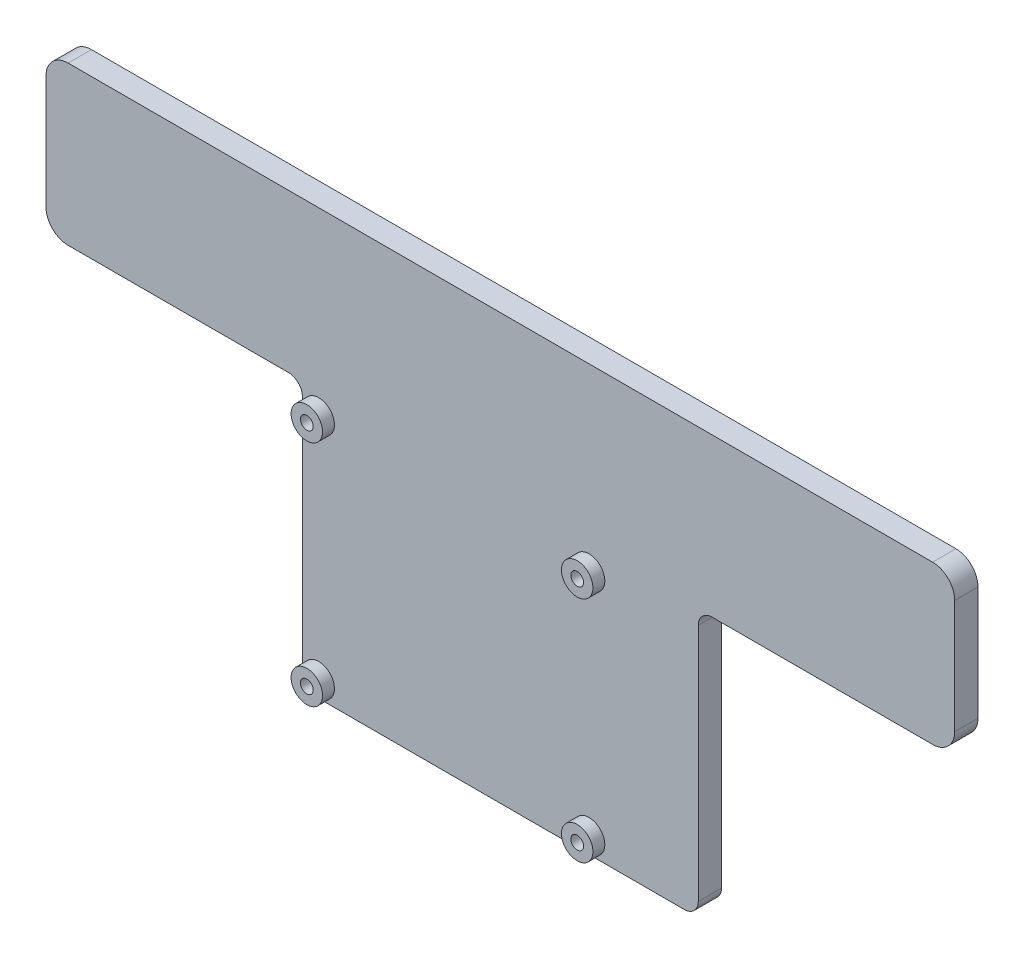
SolidWorks part; units mm, degrees
ref_plane "Ebene vorne" through (0, 0, 0) normal (0, 0, 1) x (1, 0, 0)
ref_plane "Ebene oben" through (0, 0, 0) normal (0, 1, 0) x (1, 0, 0)
ref_plane "Ebene rechts" through (0, 0, 0) normal (1, 0, 0) x (0, 0, -1)
sketch "Grundform" plane through (0, 0, 0) normal (0, 0, 1) x (1, 0, 0)
  line L0 (-93.287, 40.7816) -> (92.1707, 40.7816)
  line L2 (92.1707, 6.9168) -> (44.9039, 6.9168)
  line L4 (38.9039, -50.3878) -> (-40.0203, -50.3878)
  line L6 (-46.0203, 6.9168) -> (-93.287, 6.9168)
  line L8 (-0.5582, 76.8719) -> (-0.5582, -104.5887) construction
  line L9 (-98.0291, 36.0396) -> (-98.0291, 11.6588)
  line L10 (96.9127, 36.0396) -> (96.9127, 11.6588)
  line L11 (-43.0203, 3.9168) -> (-43.0203, -47.3878)
  line L12 (41.9039, -47.3878) -> (41.9039, 3.9168)
  line L13 (38.9039, -50.3878) -> (-40.0203, -50.3878) construction
  line L14 (41.9039, 2.6122) -> (41.9039, -47.3878) construction
  arc A0 (-93.287, 40.7816) -> (-98.0291, 36.0396) centre (-93.287, 36.0396) ccw
  arc A1 (-93.287, 6.9168) -> (-98.0291, 11.6588) centre (-93.287, 11.6588) cw
  arc A2 (92.1707, 40.7816) -> (96.9127, 36.0396) centre (92.1707, 36.0396) cw
  arc A3 (92.1707, 6.9168) -> (96.9127, 11.6588) centre (92.1707, 11.6588) ccw
  arc A4 (-46.0203, 6.9168) -> (-43.0203, 3.9168) centre (-46.0203, 3.9168) cw
  arc A5 (44.9039, 6.9168) -> (41.9039, 3.9168) centre (44.9039, 3.9168) ccw
  arc A6 (-40.0203, -50.3878) -> (-43.0203, -47.3878) centre (-40.0203, -47.3878) cw
  arc A7 (38.9039, -50.3878) -> (41.9039, -47.3878) centre (38.9039, -47.3878) ccw
  arc A8 (-43.0203, -47.3878) -> (-40.0203, -50.3878) centre (-40.0203, -47.3878) ccw construction
  circle A9 centre (-39.5203, 2.1122) radius 1.375
  circle A10 centre (18.4797, 2.1122) radius 1.375
  circle A11 centre (18.4797, -46.8878) radius 1.375
  circle A12 centre (-39.5203, -46.8878) radius 1.375
  circle A13 centre (18.4797, 2.1122) radius 1.375 construction
  circle A14 centre (18.4797, -46.8878) radius 1.375 construction
extrude "Aufsatz-Linear austragen1" add sketch "Grundform" along normal blind 5
sketch "Skizze2" plane through (0, 0, 5) normal (0, 0, 1) x (1, 0, 0)
  circle A0 centre (-39.5203, 2.1122) radius 1.375
  circle A1 centre (-39.5203, 2.1122) radius 3.375
  circle A2 centre (18.4797, 2.1122) radius 1.375
  circle A3 centre (18.4797, 2.1122) radius 3.375
  circle A4 centre (18.4797, -46.8878) radius 1.375
  circle A5 centre (18.4797, -46.8878) radius 3.375
  circle A6 centre (-39.5203, -46.8878) radius 1.375
  circle A7 centre (-39.5203, -46.8878) radius 3.375
  dimension "D1" = 2
extrude "Aufsatz-Linear austragen2" add sketch "Skizze2" along normal up to vertex (2.5544 mm away)
